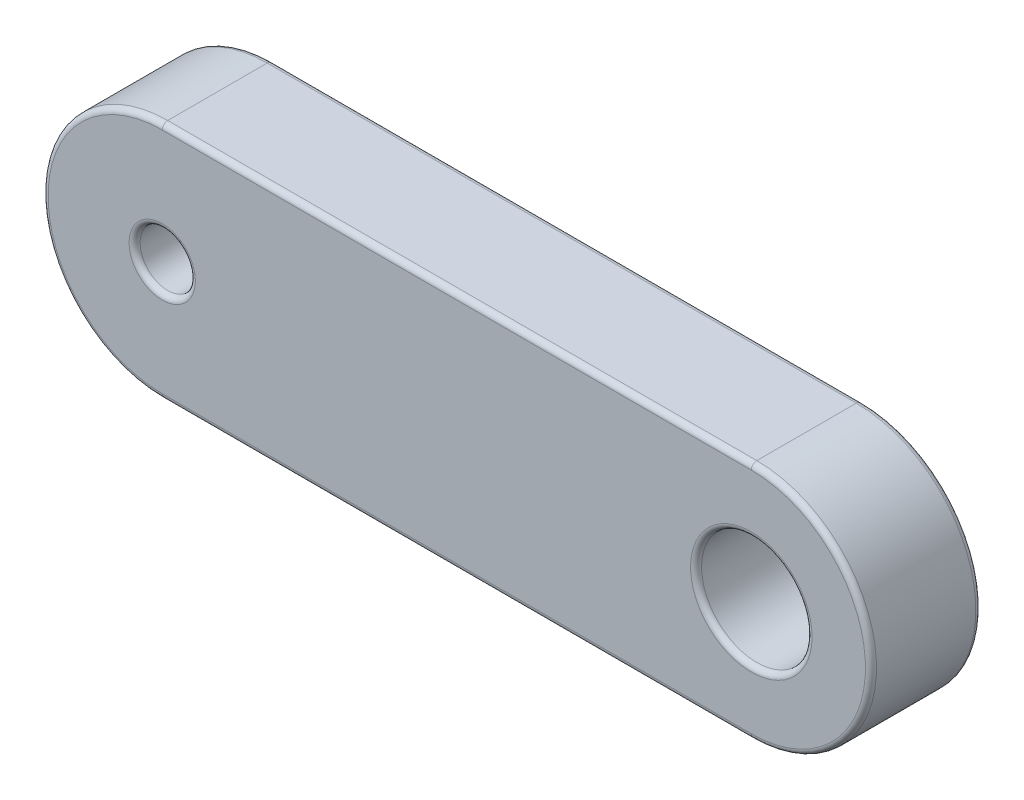
SolidWorks part; units mm, degrees
ref_plane "Ön Düzlem" through (0, 0, 0) normal (0, 0, 1) x (1, 0, 0)
ref_plane "Üst Düzlem" through (0, 0, 0) normal (0, 1, 0) x (1, 0, 0)
ref_plane "Sağ Düzlem" through (0, 0, 0) normal (1, 0, 0) x (0, 0, -1)
sketch "Sketch1" plane through (0, 0, 0) normal (0, 0, 1) x (1, 0, 0)
  line L0 (-8, 0) -> (8, 0) construction
  line L1 (-8, 3.25) -> (8, 3.25)
  line L2 (-8, -3.25) -> (8, -3.25)
  arc A0 (-8, 3.25) -> (-8, -3.25) centre (-8, 0) ccw
  arc A1 (8, -3.25) -> (8, 3.25) centre (8, 0) ccw
  circle A2 centre (-8, 0) radius 0.75
  circle A3 centre (8, 0) radius 1.5
  point P2 (0, 0)
  dimension "D3" = 1.5
  dimension "D4" = 3
  dimension "D1" = 16
  dimension "D2" = 6.5
extrude "Boss-Extrude1" add sketch "Sketch1" along normal mid plane 3
fillet "Fillet1" radius 0.15 12 edges at (9.5, 0, -1.5) (-7.25, 0, -1.5) (0, -3.25, -1.5) (11.25, 0, -1.5) (0, 3.25, -1.5) (-11.25, 0, -1.5) (9.5, 0, 1.5) (0, 3.25, 1.5) (11.25, 0, 1.5) (0, -3.25, 1.5) (-11.25, 0, 1.5) (-7.25, 0, 1.5)
